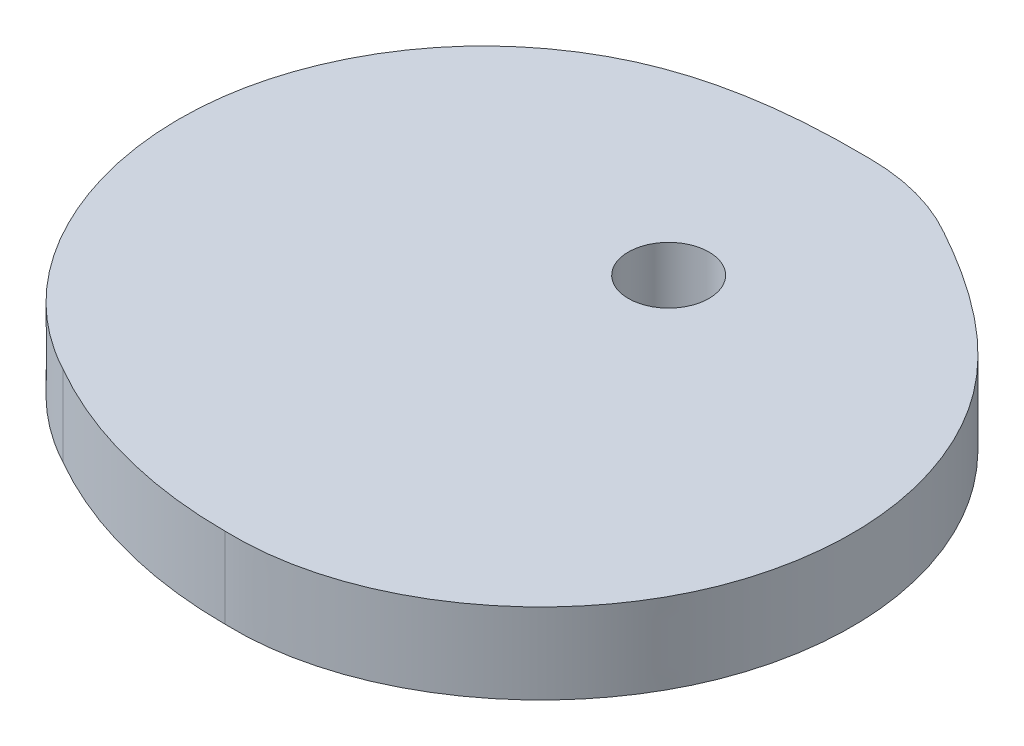
SolidWorks part; units mm, degrees
ref_plane "Front Plane" through (0, 0, 0) normal (0, 0, 1) x (1, 0, 0)
ref_plane "Top Plane" through (0, 0, 0) normal (0, 1, 0) x (1, 0, 0)
ref_plane "Right Plane" through (0, 0, 0) normal (1, 0, 0) x (0, 0, -1)
sketch "Sketch2" plane through (0, 0, 0) normal (0, 1, 0) x (1, 0, 0)
  arc A1 (-27.5, -47.6314) -> (0, -55) centre (0, 0) ccw
  circle A2 centre (0, 0) radius 5
  arc A5 (12.5, 21.6506) -> (0, 25) centre (0, 0) ccw
  spline S0 degree 3 poles (0, 25) (-8.3352, 25.1358) (-23.1852, 23.8489) (-40.5362, 10.6089) (-52.2585, -16.1981) (-41.4631, -40.1722) (-27.5, -47.6314) knots 0 0 0 0 0.233107 0.392178 0.578701 1 1 1 1
  spline S1 degree 3 poles (0, -55) (15.822, -55.5217) (37.1582, -40.1572) (40.4098, -11.0806) (32.0034, 9.0612) (19.7864, 17.6006) (12.5, 21.6506) knots 0 0 0 0 0.421299 0.607822 0.766893 1 1 1 1
  point P3 (0, 0)
  point P13 (0, 0)
  point P20 (0, 0)
  point P23 (0, 0)
  point P36 (0, 0)
  dimension "D11" = 55
extrude "Boss-Extrude1" add sketch "Sketch2" along normal blind 10
